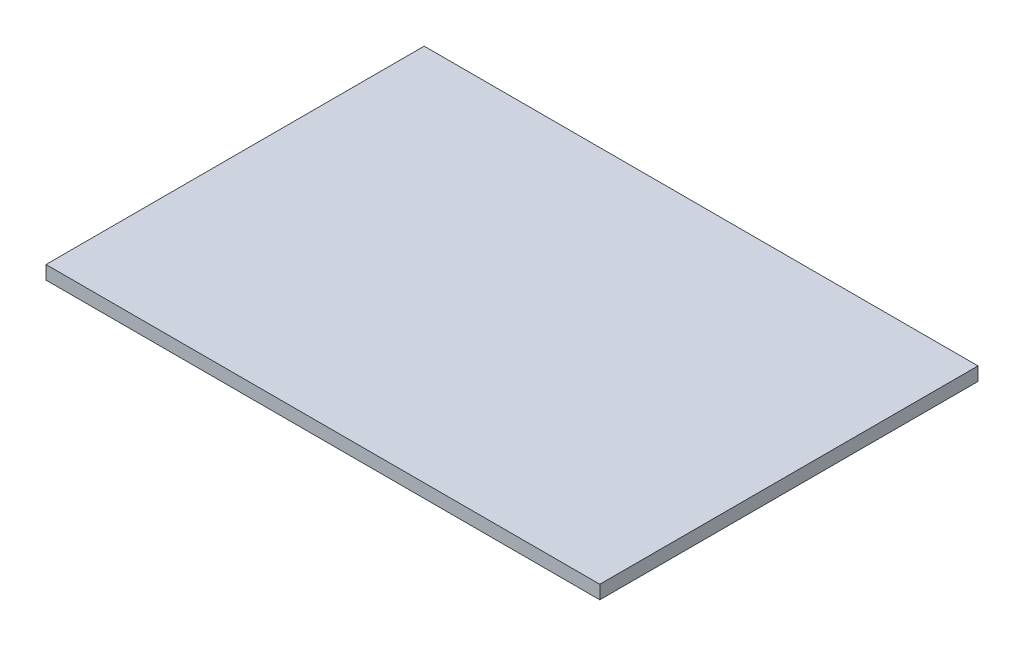
SolidWorks part; units mm, degrees
ref_plane "Спереди" through (0, 0, 0) normal (0, 0, 1) x (1, 0, 0)
ref_plane "Сверху" through (0, 0, 0) normal (0, 1, 0) x (1, 0, 0)
ref_plane "Справа" through (0, 0, 0) normal (1, 0, 0) x (0, 0, -1)
sketch "Эскиз1" plane through (0, 0, 0) normal (0, 1, 0) x (1, 0, 0)
  line L1 (0, 0) -> (41, 0)
  line L2 (0, 0) -> (0, 28)
  line L3 (0, 28) -> (41, 28)
  line L4 (41, 0) -> (41, 28)
  dimension "D1" = 28
  dimension "D2" = 41
extrude "Бобышка-Вытянуть1" add sketch "Эскиз1" along normal blind 1
